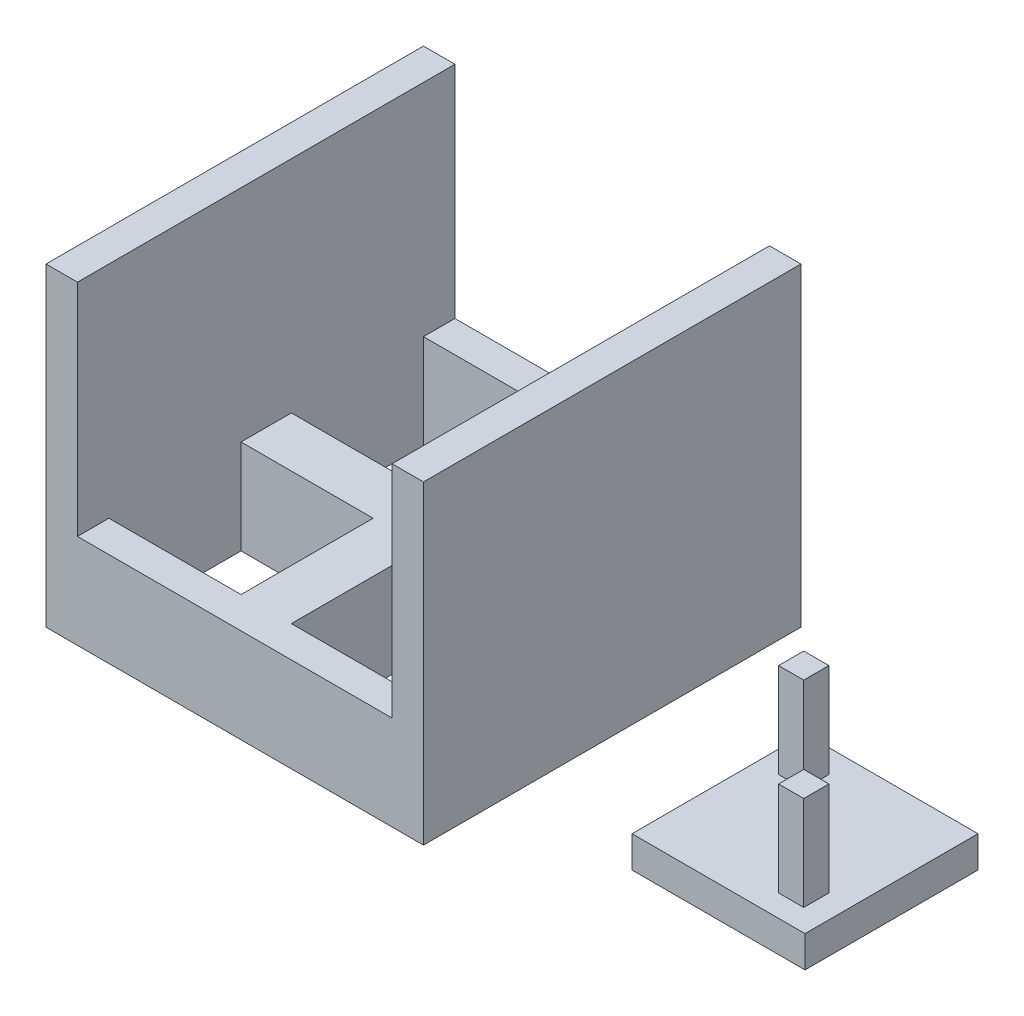
SolidWorks part; units mm, degrees
ref_plane "Front Plane" through (0, 0, 0) normal (0, 0, 1) x (1, 0, 0)
ref_plane "Top Plane" through (0, 0, 0) normal (0, 1, 0) x (1, 0, 0)
ref_plane "Right Plane" through (0, 0, 0) normal (1, 0, 0) x (0, 0, -1)
sketch "Sketch1" plane through (0, 0, 0) normal (0, 1, 0) x (1, 0, 0)
  line L1 (-30, 30) -> (30, 30)
  line L2 (-30, 30) -> (-30, -30)
  line L3 (-30, -30) -> (30, -30)
  line L4 (30, 30) -> (30, -30)
  line L5 (-30, 30) -> (30, -30) construction
  line L6 (-30, -30) -> (30, 30) construction
  point P0 (0, 0)
  dimension "D1" = 60
  dimension "D2" = 60
extrude "Boss-Extrude1" add sketch "Sketch1" along normal blind 50
sketch "Sketch2" plane through (0, 0, 0) normal (0, 1, 0) x (1, 0, 0)
  line L1 (-25, 25) -> (25, 25)
  line L2 (-25, 25) -> (-25, -25)
  line L3 (-25, -25) -> (25, -25)
  line L4 (25, 25) -> (25, -25)
  line L5 (-25, 25) -> (25, -25) construction
  line L6 (-25, -25) -> (25, 25) construction
  point P0 (0, 0)
  dimension "D1" = 50
  dimension "D2" = 50
extrude "Cut-Extrude1" cut sketch "Sketch2" along normal blind 50
sketch "Sketch3" plane through (0, 0, 0) normal (0, 1, 0) x (1, 0, 0)
  line L1 (-4, 28.3926) -> (4, 28.3926)
  line L2 (-4, 28.3926) -> (-4, -28.3926)
  line L3 (-4, -28.3926) -> (4, -28.3926)
  line L4 (4, 28.3926) -> (4, -28.3926)
  line L5 (-4, 28.3926) -> (4, -28.3926) construction
  line L6 (-4, -28.3926) -> (4, 28.3926) construction
  point P0 (0, 0)
  dimension "D1" = 8
extrude "Boss-Extrude2" add sketch "Sketch3" along normal blind 50
sketch "Sketch5" plane through (0, 0, 0) normal (0, 1, 0) x (1, 0, 0)
  line L1 (-28.208, 4) -> (28.208, 4)
  line L2 (-28.208, 4) -> (-28.208, -4)
  line L3 (-28.208, -4) -> (28.208, -4)
  line L4 (28.208, 4) -> (28.208, -4)
  line L5 (-28.208, 4) -> (28.208, -4) construction
  line L6 (-28.208, -4) -> (28.208, 4) construction
  point P0 (0, 0)
  dimension "D1" = 8
extrude "Boss-Extrude3" add sketch "Sketch5" along normal blind 50
sketch "Sketch6" plane through (0, 0, 0) normal (0, 0, 1) x (1, 0, 0)
  line L0 (-30, 50) -> (30, 50) construction
  line L1 (25, 50) -> (-25, 50)
  line L2 (25, 50) -> (25, 15)
  line L3 (25, 15) -> (-25, 15)
  line L4 (-25, 50) -> (-25, 15)
  line L5 (30, 50) -> (30, 0) construction
  line L6 (-30, 50) -> (-30, 0) construction
  dimension "D1" = 5
  dimension "D2" = 35
  dimension "D3" = 50
  dimension "D4" = 5
extrude "Cut-Extrude2" cut sketch "Sketch6" against normal blind 30 and the other way blind 30
sketch "Sketch7" plane through (0, 0, 0) normal (0, 1, 0) x (1, 0, 0)
  line L0 (30, -30) -> (30, 30) construction
  line L1 (50, 10.6454) -> (77.5, 10.6454)
  line L2 (50, 10.6454) -> (50, -16.8546)
  line L3 (50, -16.8546) -> (77.5, -16.8546)
  line L4 (77.5, 10.6454) -> (77.5, -16.8546)
  line L5 (50, 10.6454) -> (77.5, -16.8546) construction
  line L6 (50, -16.8546) -> (77.5, 10.6454) construction
  point P0 (63.75, -3.1046)
  dimension "D1" = 27.5
  dimension "D2" = 27.5
  dimension "D3" = 20
extrude "Boss-Extrude4" add sketch "Sketch7" along normal blind 5 separate body
sketch "Sketch9" plane through (0, 0, 0) normal (0, 1, 0) x (1, 0, 0)
  line L0 (77.5, -16.8546) -> (77.5, 10.6454) construction
  line L1 (57.5, 2.9454) -> (53.5, 2.9454)
  line L2 (57.5, 2.9454) -> (57.5, 6.9454)
  line L3 (57.5, 6.9454) -> (53.5, 6.9454)
  line L4 (53.5, 2.9454) -> (53.5, 6.9454)
  line L5 (57.5, 2.9454) -> (53.5, 6.9454) construction
  line L6 (57.5, 6.9454) -> (53.5, 2.9454) construction
  line L7 (77.5, 10.6454) -> (50, 10.6454) construction
  point P0 (55.5, 4.9454)
  dimension "D1" = 20
  dimension "D2" = 4
  dimension "D3" = 3.7
  dimension "D4" = 4
extrude "Boss-Extrude5" add sketch "Sketch9" along normal blind 20
sketch "Sketch10" plane through (0, 0, 0) normal (0, 1, 0) x (1, 0, 0)
  line L0 (77.5, -16.8546) -> (77.5, 10.6454) construction
  line L1 (69.8, -9.3546) -> (73.8, -9.3546)
  line L2 (69.8, -9.3546) -> (69.8, -13.3546)
  line L3 (69.8, -13.3546) -> (73.8, -13.3546)
  line L4 (73.8, -9.3546) -> (73.8, -13.3546)
  line L5 (69.8, -9.3546) -> (73.8, -13.3546) construction
  line L6 (69.8, -13.3546) -> (73.8, -9.3546) construction
  line L7 (77.5, 10.6454) -> (50, 10.6454) construction
  point P0 (71.8, -11.3546)
  dimension "D1" = 3.7
  dimension "D2" = 20
  dimension "D3" = 4
  dimension "D4" = 4
extrude "Boss-Extrude6" add sketch "Sketch10" along normal blind 20
